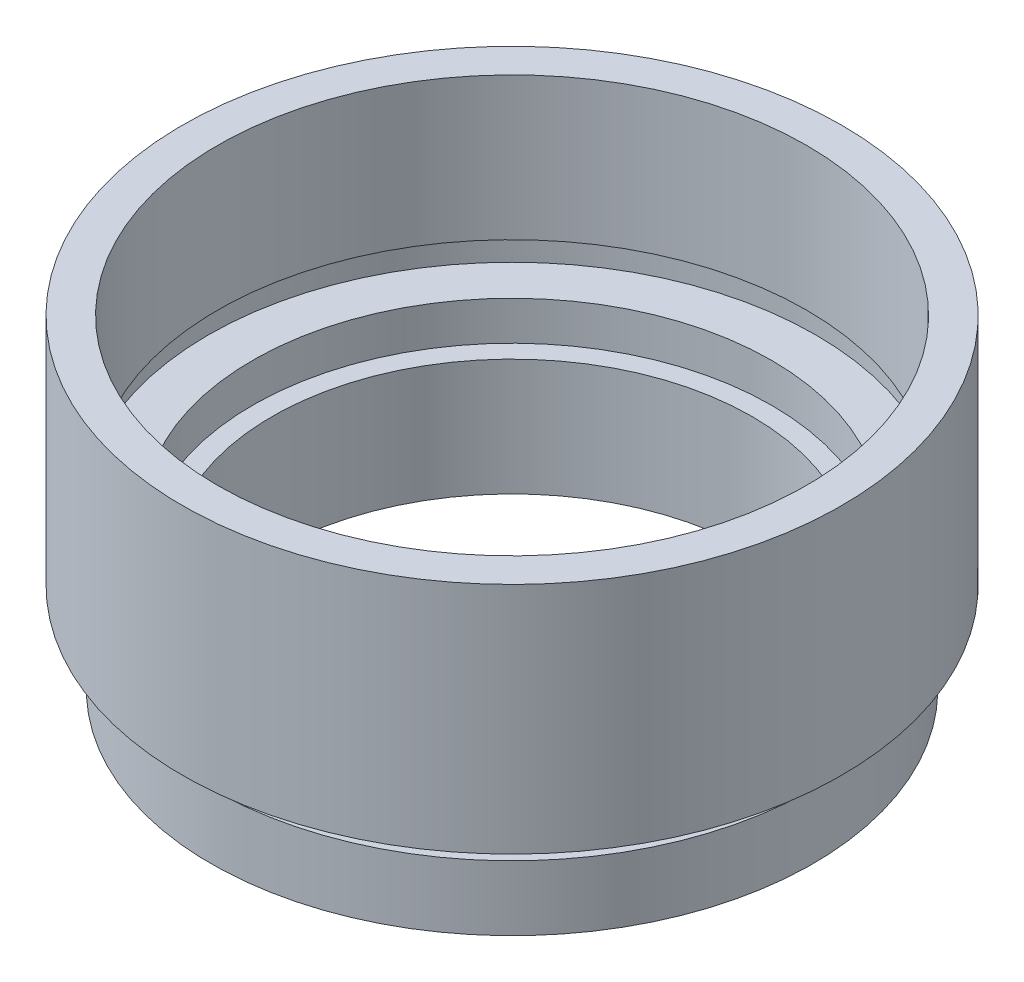
SolidWorks part; units mm, degrees
ref_plane "前视基准面" through (0, 0, 0) normal (0, 0, 1) x (1, 0, 0)
ref_plane "上视基准面" through (0, 0, 0) normal (0, 1, 0) x (1, 0, 0)
ref_plane "右视基准面" through (0, 0, 0) normal (1, 0, 0) x (0, 0, -1)
sketch "草图1" plane through (0, 0, 0) normal (0, 0, 1) x (1, 0, 0)
  line L0 (0, 0) -> (0, 21.8535) construction
  line L1 (9.25, 0) -> (11.6, 0)
  line L2 (11.6, 0) -> (11.6, 2.5)
  line L3 (11.6, 2.5) -> (11.1, 2.5)
  line L4 (11.1, 2.5) -> (11.1, 3.5)
  line L5 (11.1, 3.5) -> (12.7, 3.5)
  line L6 (12.7, 3.5) -> (12.7, 12.5)
  line L7 (12.7, 12.5) -> (11.35, 12.5)
  line L8 (11.35, 12.5) -> (11.35, 7)
  line L9 (11.35, 7) -> (11.7, 7)
  line L10 (11.7, 7) -> (11.7, 6)
  line L11 (11.7, 6) -> (10, 6)
  line L12 (10, 6) -> (10, 4.5)
  line L13 (10, 4.5) -> (9.25, 4.5)
  line L14 (9.25, 0) -> (9.25, 4.5)
  dimension "D1" = 12.5
  dimension "D2" = 12.7
  dimension "D3" = 11.35
  dimension "D4" = 10
  dimension "D5" = 1
  dimension "D6" = 1.5
  dimension "D7" = 9.25
  dimension "D8" = 11.6
  dimension "D9" = 1
  dimension "D10" = 3.5
  dimension "D11" = 4.5
  dimension "D12" = 11.7
  dimension "D13" = 11.1
revolve "旋转1" add sketch "草图1" angle 360 about L0
cosmetic thread "装饰螺纹线11" parameters "D2"=22
cosmetic thread "装饰螺纹线12" parameters "D2"=23.2
